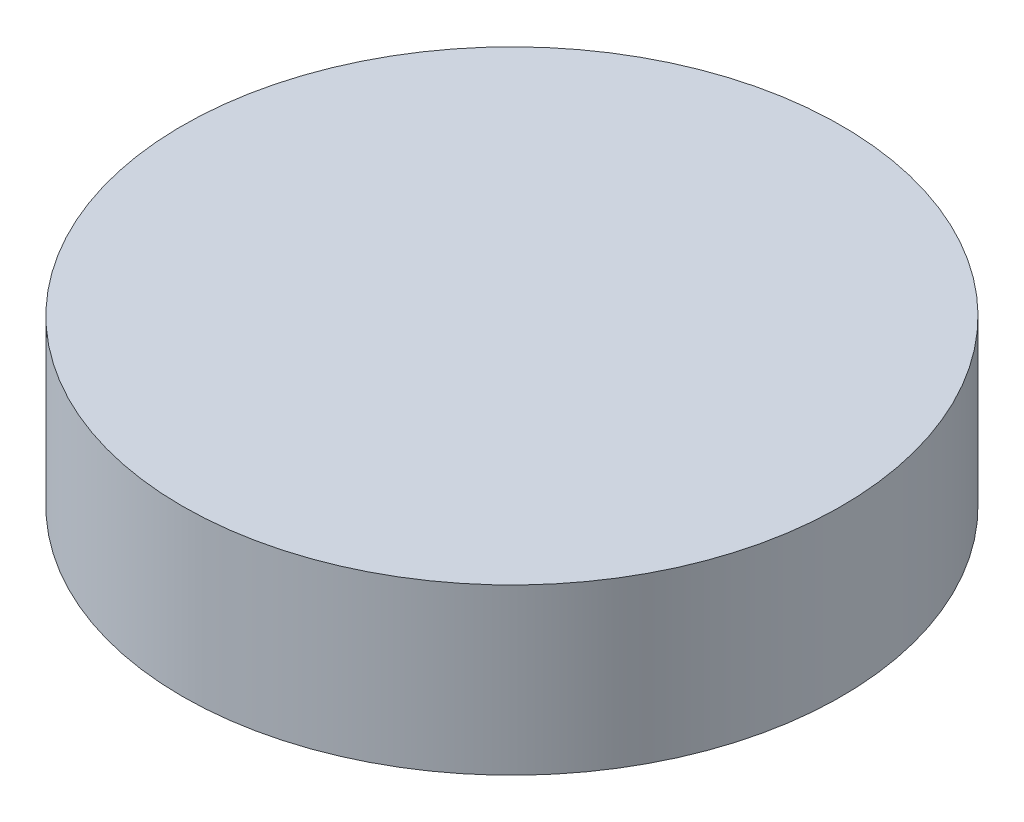
SolidWorks part; units mm, degrees
ref_plane "前视基准面" through (0, 0, 0) normal (0, 0, 1) x (1, 0, 0)
ref_plane "上视基准面" through (0, 0, 0) normal (0, 1, 0) x (1, 0, 0)
ref_plane "右视基准面" through (0, 0, 0) normal (1, 0, 0) x (0, 0, -1)
sketch "草图1" plane through (0, 0, 0) normal (0, 1, 0) x (1, 0, 0)
  circle A0 centre (0, 0) radius 25.4
  dimension "D1" = 50.8
extrude "凸台-拉伸1" add sketch "草图1" along normal blind 12.7
